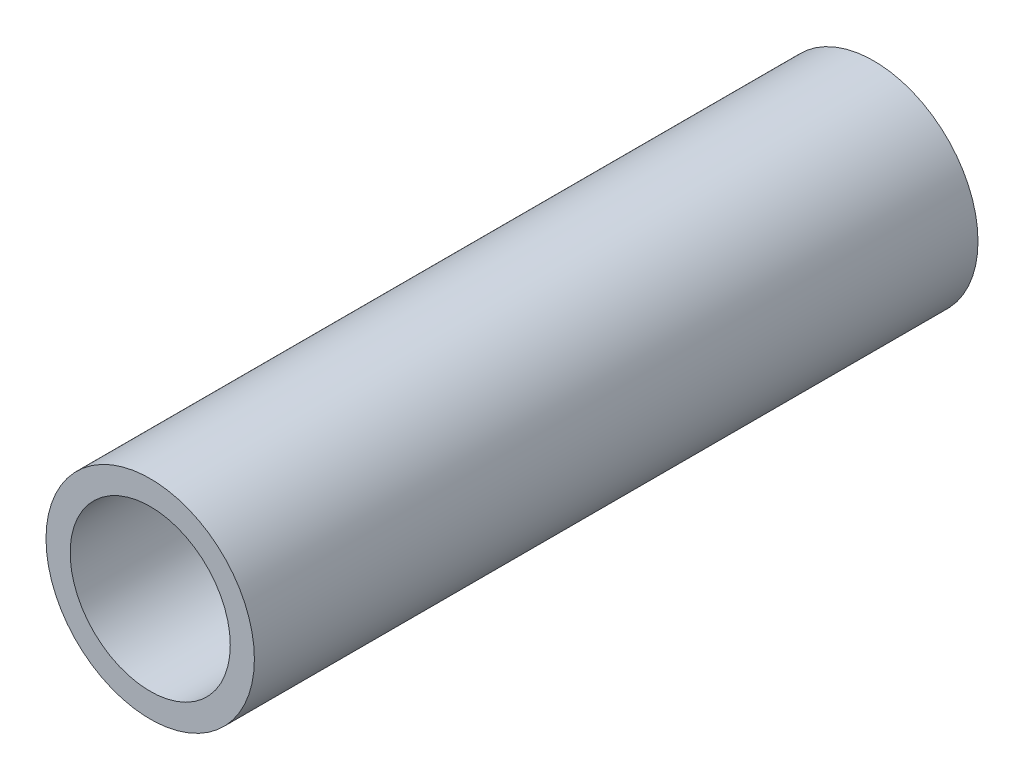
SolidWorks part; units mm, degrees
ref_plane "Alzado" through (0, 0, 0) normal (0, 0, 1) x (1, 0, 0)
ref_plane "Planta" through (0, 0, 0) normal (0, 1, 0) x (1, 0, 0)
ref_plane "Vista lateral" through (0, 0, 0) normal (1, 0, 0) x (0, 0, -1)
sketch "Croquis1" plane through (0, 0, 0) normal (0, 0, 1) x (1, 0, 0)
  circle A0 centre (0, 0) radius 21.6
  circle A1 centre (0, 0) radius 16.6
  dimension "D1" = 5
  dimension "D2" = 33.2
  dimension "D3" = 43.2
extrude "Saliente-Extruir1" add sketch "Croquis1" along normal blind 150
